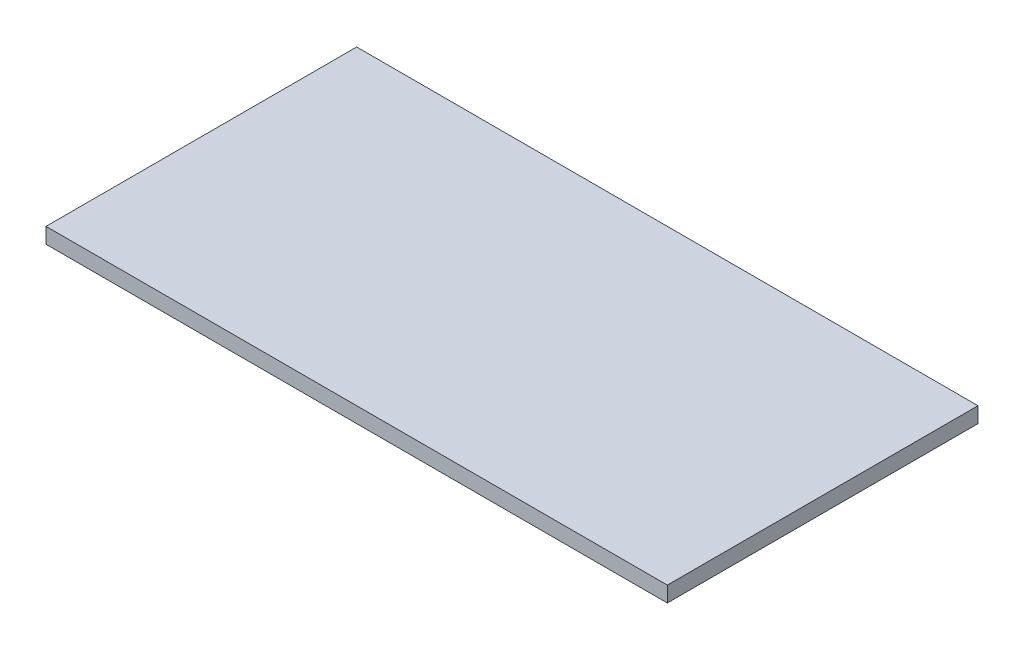
SolidWorks part; units mm, degrees
ref_plane "Front Plane" through (0, 0, 0) normal (0, 0, 1) x (1, 0, 0)
ref_plane "Top Plane" through (0, 0, 0) normal (0, 1, 0) x (1, 0, 0)
ref_plane "Right Plane" through (0, 0, 0) normal (1, 0, 0) x (0, 0, -1)
sketch "Sketch1" plane through (0, 0, 0) normal (0, 1, 0) x (1, 0, 0)
  line L1 (0, 0) -> (254, 0)
  line L2 (0, 0) -> (0, 127)
  line L3 (0, 127) -> (254, 127)
  line L4 (254, 0) -> (254, 127)
  dimension "D1" = 127
  dimension "D2" = 254
extrude "Boss-Extrude1" add sketch "Sketch1" along normal blind 6.35
